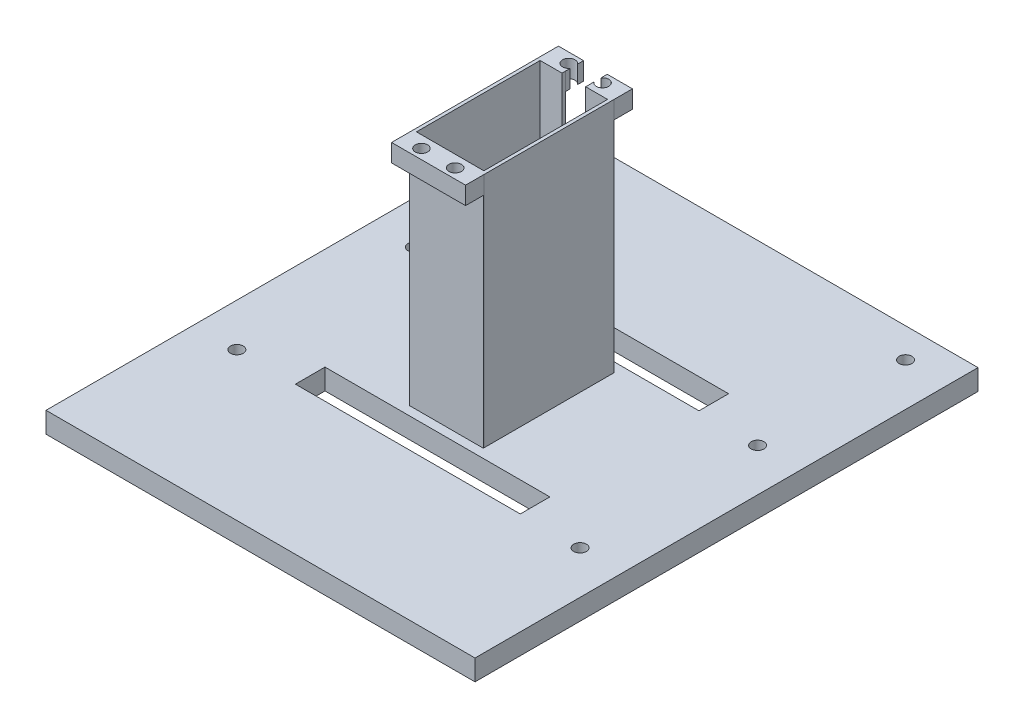
SolidWorks part; units mm, degrees
ref_plane "Front Plane" through (0, 0, 0) normal (0, 0, 1) x (1, 0, 0)
ref_plane "Top Plane" through (0, 0, 0) normal (0, 1, 0) x (1, 0, 0)
ref_plane "Right Plane" through (0, 0, 0) normal (1, 0, 0) x (0, 0, -1)
sketch "Sketch1" plane through (0, 0, 0) normal (0, 1, 0) x (1, 0, 0)
  line L1 (72.5, -85) -> (-72.5, -85)
  line L2 (72.5, -85) -> (72.5, 85)
  line L3 (72.5, 85) -> (-72.5, 85)
  line L4 (-72.5, -85) -> (-72.5, 85)
  line L5 (72.5, -85) -> (-72.5, 85) construction
  line L6 (72.5, 85) -> (-72.5, -85) construction
  line L7 (-12.5, 85) -> (12.5, 85)
  point P0 (0, 0)
  point P10 (0, 85)
  dimension "D1" = 145
  dimension "D2" = 170
extrude "Boss-Extrude1" add sketch "Sketch1" along normal blind 7
sketch "Sketch2" plane through (0, 7, 0) normal (0, 1, 0) x (1, 0, 0)
  line L4 (12.5, 22) -> (-12.5, 22)
  line L5 (-12.5, -22) -> (12.5, -22)
  line L6 (12.5, 22) -> (12.5, -22)
  line L7 (-12.5, 22) -> (-12.5, -22)
  point P1 (0, 22)
  point P5 (-12.5, 0)
  point P8 (12.5, 0)
  dimension "D1" = 44
  dimension "D2" = 44
  dimension "D3" = 25
  dimension "D4" = 25
extrude "Boss-Extrude2" add sketch "Sketch2" along normal blind 80
sketch "Sketch3" plane through (0, 87, 0) normal (0, 1, 0) x (1, 0, 0)
  line L8 (-11.4, 20.9) -> (-11.4, -20.9)
  line L9 (-11.4, -20.9) -> (11.4, -20.9)
  line L10 (11.4, -20.9) -> (11.4, 20.9)
  line L11 (11.4, 20.9) -> (-11.4, 20.9)
  line L12 (-11.4, 20.9) -> (-11.4, -20.9)
  line L13 (-11.4, -20.9) -> (11.4, -20.9)
  line L14 (11.4, -20.9) -> (11.4, 20.9)
  line L15 (11.4, 20.9) -> (-11.4, 20.9)
  dimension "D1" = 1.1
extrude "Cut-Extrude1" cut sketch "Sketch3" against normal blind 28
sketch "Sketch4" plane through (0, 87, 0) normal (0, 1, 0) x (1, 0, 0)
  line L0 (12.5, 22) -> (-12.5, 22) construction
  line L1 (-4, 22) -> (4, 22)
  line L2 (-4, 22) -> (-4, 20.9)
  line L3 (-4, 20.9) -> (4, 20.9)
  line L4 (4, 22) -> (4, 20.9)
  line L5 (11.4, 20.9) -> (-11.4, 20.9) construction
  point P8 (0, 22)
  dimension "D1" = 8
extrude "Cut-Extrude2" cut sketch "Sketch4" against normal through all
sketch "Sketch5" plane through (0, 0, 22) normal (0, 0, 1) x (1, 0, 0)
  line L1 (-12.5, 87) -> (12.5, 87)
  line L2 (-12.5, 87) -> (-12.5, 7)
  line L3 (-12.5, 7) -> (12.5, 7)
  line L4 (12.5, 87) -> (12.5, 7)
extrude "Boss-Extrude3" add sketch "Sketch5" along normal blind 6.2
sketch "Sketch8" plane through (0, 87, 0) normal (0, 1, 0) x (1, 0, 0)
  line L0 (0, 31.7911) -> (0, -40.9045) construction
  line L2 (-11.4, -20.9) -> (11.4, -20.9) construction
  line L4 (0, -20.9) -> (11.4, -20.9)
  line L5 (-7.8, -24.9) -> (-7.8, -28.2)
  line L6 (-12.5, -28.2) -> (12.5, -28.2) construction
  line L7 (-3.6, -24.9) -> (-3.6, -28.2)
  line L8 (3.6, -24.9) -> (3.6, -28.2)
  line L9 (7.8, -24.9) -> (7.8, -28.2)
  line L10 (12.5, -28.2) -> (-12.5, -28.2) construction
  line L11 (7.8, -28.2) -> (3.6, -28.2)
  line L12 (-3.6, -28.2) -> (-7.8, -28.2)
  circle A0 centre (5.7, -24.9) radius 2.1
  circle A1 centre (-5.7, -24.9) radius 2.1
  point P8 (5.7, -20.9)
  dimension "D1" = 4.2
  dimension "D2" = 4
extrude "Cut-Extrude3" cut sketch "Sketch8" against normal blind 6 contours A1 | A0
sketch "Sketch13" plane through (0, 0, 28.2) normal (0, 0, 1) x (1, 0, 0)
  line L0 (-12.5, 87) -> (-12.5, 7) construction
  line L1 (-12.5, 81) -> (12.5, 81)
  line L2 (-12.5, 81) -> (-12.5, 7)
  line L3 (-12.5, 7) -> (12.5, 7)
  line L4 (12.5, 81) -> (12.5, 7)
  line L5 (12.5, 87) -> (-12.5, 87) construction
  line L6 (12.5, 87) -> (-12.5, 87)
  line M6 (-12.5, 87) -> (-12.5, 7)
  line M7 (-12.5, 7) -> (12.5, 7)
  line M8 (12.5, 7) -> (12.5, 87)
  dimension "D1" = 6
extrude "Cut-Extrude11" cut sketch "Sketch13" against normal blind 6 contours L1 M6 M7 M8
sketch "Sketch15" plane through (0, 0, -22) normal (0, 0, -1) x (-1, 0, 0)
  line L0 (-4, 7) -> (-4, 87) construction
  line L1 (-12.5, 87) -> (-4, 87)
  line L2 (-12.5, 87) -> (-12.5, 81)
  line L3 (-12.5, 81) -> (-4, 81)
  line L4 (-4, 87) -> (-4, 81)
  line L5 (0, 46.7473) -> (0, -10.4442) construction
  line L6 (12.5, 81) -> (4, 81)
  line L7 (4, 87) -> (4, 81)
  line L8 (12.5, 87) -> (12.5, 81)
  line L9 (12.5, 87) -> (4, 87)
  dimension "D1" = 6
extrude "Boss-Extrude6" add sketch "Sketch15" along normal blind 6.2
sketch "Sketch16" plane through (0, 87, 0) normal (0, 1, 0) x (1, 0, 0)
  line L0 (-29.4293, 0) -> (27.0134, 0) construction
  circle A0 centre (5.7, -24.9) radius 2.1 construction
  circle A1 centre (-5.7, -24.9) radius 2.1 construction
  circle A2 centre (5.7, -24.9) radius 2.1
  circle A3 centre (-5.7, -24.9) radius 2.1
  circle A4 centre (5.7, 24.9) radius 2.1
  circle A5 centre (-5.7, 24.9) radius 2.1
extrude "Cut-Extrude12" cut sketch "Sketch16" against normal blind 6.2
sketch "Sketch17" plane through (0, 7, 0) normal (0, 1, 0) x (1, 0, 0)
  line L0 (-72.5, -85) -> (-72.5, 85) construction
  line L1 (72.5, 85) -> (-72.5, 85) construction
  line L2 (0, 94.7123) -> (0, -108.8325) construction
  circle A0 centre (-58, 75) radius 2.15
  circle A1 centre (-58, 25) radius 2.15
  circle A2 centre (-58, -35) radius 2.15
  circle A3 centre (58, -35) radius 2.15
  circle A4 centre (58, 25) radius 2.15
  circle A5 centre (58, 75) radius 2.15
  dimension "D1" = 4.3
  dimension "D2" = 14.5
  dimension "D3" = 50
  dimension "D4" = 60
  dimension "D5" = 10
extrude "Cut-Extrude13" cut sketch "Sketch17" against normal through all
sketch "Sketch18" plane through (0, 7, 0) normal (0, 1, 0) x (1, 0, 0)
  line L0 (-102.7519, 0) -> (101.4174, 0) construction
  line L1 (38, -35.2) -> (-38, -35.2)
  line L2 (38, -35.2) -> (38, -25.2)
  line L3 (38, -25.2) -> (-38, -25.2)
  line L4 (-72.5, 85) -> (-72.5, -85)
  line L5 (-72.5, -85) -> (72.5, -85)
  line L6 (72.5, -85) -> (72.5, 85)
  line L7 (72.5, 85) -> (-72.5, 85)
  line L8 (-72.5, 85) -> (-72.5, -85)
  line L9 (-72.5, -85) -> (72.5, -85)
  line L10 (72.5, -85) -> (72.5, 85)
  line L11 (72.5, 85) -> (-72.5, 85)
  line L12 (-38, -35.2) -> (-38, -25.2)
  line L13 (38, -35.2) -> (-38, -25.2) construction
  line L14 (38, -25.2) -> (-38, -35.2) construction
  line L15 (38, 25.2) -> (-38, 35.2) construction
  line L16 (-12.5, -22.2) -> (12.5, -22.2) construction
  line L17 (-12.5, -22.2) -> (12.5, -22.2)
  line L18 (38, 35.2) -> (-38, 25.2) construction
  line L19 (-12.5, 22.2) -> (12.5, 22.2)
  line L20 (-38, 35.2) -> (-38, 25.2)
  line L21 (38, 25.2) -> (-38, 25.2)
  line L22 (38, 35.2) -> (38, 25.2)
  line L23 (38, 35.2) -> (-38, 35.2)
  circle A0 centre (58, -35) radius 2.15 construction
  circle A1 centre (-58, -35) radius 2.15 construction
  circle A2 centre (58, 25) radius 2.15 construction
  circle A3 centre (-58, 25) radius 2.15 construction
  circle A4 centre (58, 75) radius 2.15 construction
  circle A5 centre (-58, 75) radius 2.15 construction
  circle A6 centre (58, -35) radius 2.15
  circle A7 centre (-58, -35) radius 2.15
  circle A8 centre (58, 25) radius 2.15
  circle A9 centre (-58, 25) radius 2.15
  circle A10 centre (58, 75) radius 2.15
  circle A11 centre (-58, 75) radius 2.15
  point P20 (0, -30.2)
  dimension "D2" = 8
  dimension "D3" = 20
  dimension "D4" = 10
  dimension "D1" = 0
extrude "Cut-Extrude14" cut sketch "Sketch18" against normal through all contours L22 L23 L20 L21 | L12 L1 L2 L3
